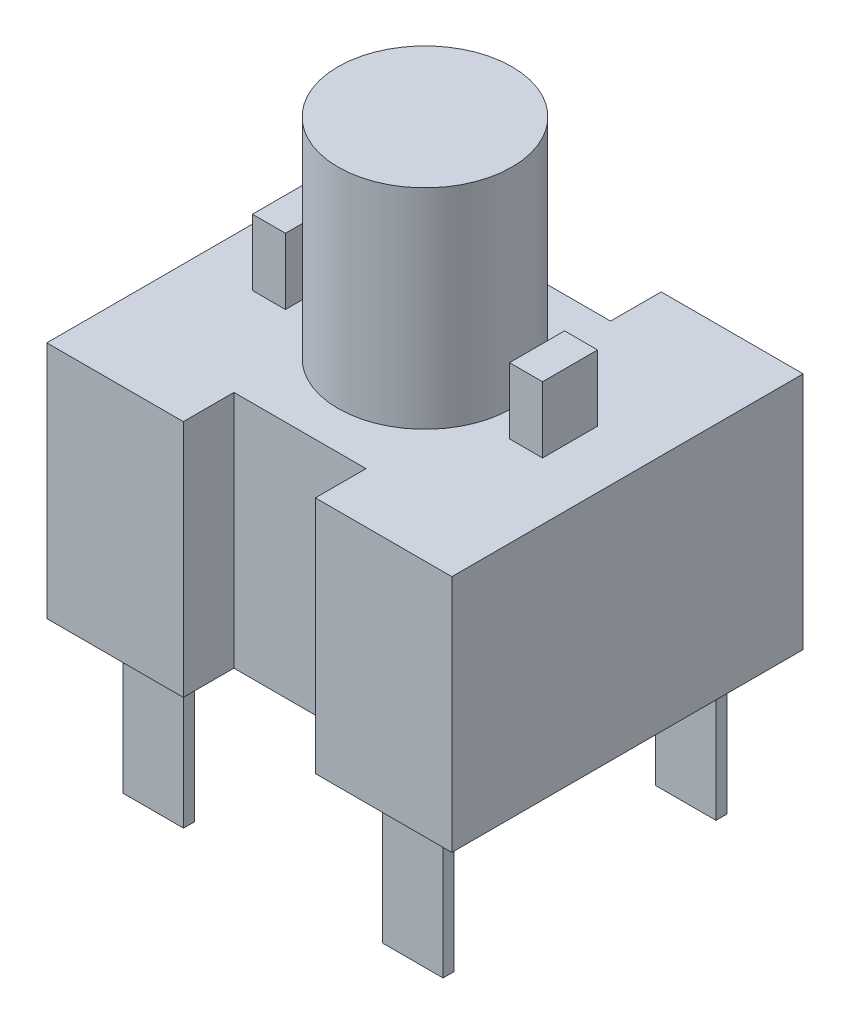
SolidWorks part; units mm, degrees
ref_plane "Front Plane" through (0, 0, 0) normal (0, 0, 1) x (1, 0, 0)
ref_plane "Top Plane" through (0, 0, 0) normal (0, 1, 0) x (1, 0, 0)
ref_plane "Right Plane" through (0, 0, 0) normal (1, 0, 0) x (0, 0, -1)
sketch "Sketch1" plane through (0, 0, 0) normal (0, 1, 0) x (1, 0, 0)
  line L1 (-9.2, -7.98) -> (9.2, -7.98)
  line L2 (-9.2, -7.98) -> (-9.2, 7.98)
  line L3 (-9.2, 7.98) -> (9.2, 7.98)
  line L4 (9.2, -7.98) -> (9.2, 7.98)
  line L5 (-9.2, -7.98) -> (9.2, 7.98) construction
  line L6 (-9.2, 7.98) -> (9.2, -7.98) construction
  point P0 (0, 0)
  dimension "D1" = 18.4
  dimension "D2" = 15.96
extrude "Boss-Extrude1" add sketch "Sketch1" along normal blind 10.85
sketch "Sketch2" plane through (0, 0, 0) normal (0, -1, 0) x (1, 0, 0)
  line L0 (0, 0) -> (-9.2, 0) construction
  line L1 (-7.27, -5.95) -> (-4.52, -5.95)
  line L2 (-7.27, -5.95) -> (-7.27, -6.45)
  line L3 (-7.27, -6.45) -> (-4.52, -6.45)
  line L4 (-4.52, -5.95) -> (-4.52, -6.45)
  line L5 (-9.2, -7.98) -> (-9.2, 7.98) construction
  line L6 (-4.52, 5.95) -> (-4.52, 6.45)
  line L7 (-7.27, 6.45) -> (-4.52, 6.45)
  line L8 (-7.27, 5.95) -> (-7.27, 6.45)
  line L9 (-7.27, 5.95) -> (-4.52, 5.95)
  line L10 (0, 0) -> (0, 7.98) construction
  line L11 (-9.2, 7.98) -> (9.2, 7.98) construction
  line L12 (4.52, -5.95) -> (4.52, -6.45)
  line L13 (7.27, -6.45) -> (4.52, -6.45)
  line L14 (7.27, -5.95) -> (7.27, -6.45)
  line L15 (7.27, -5.95) -> (4.52, -5.95)
  line L16 (7.27, 5.95) -> (4.52, 5.95)
  line L17 (7.27, 5.95) -> (7.27, 6.45)
  line L18 (7.27, 6.45) -> (4.52, 6.45)
  line L19 (4.52, 5.95) -> (4.52, 6.45)
  dimension "D1" = 0.5
  dimension "D2" = 2.75
  dimension "D3" = 12.9
  dimension "D4" = 14.54
extrude "Boss-Extrude2" add sketch "Sketch2" along normal blind 6.67
sketch "Sketch3" plane through (0, 10.85, 0) normal (0, 1, 0) x (1, 0, 0)
  line L0 (9.2, 7.98) -> (-9.2, 7.98) construction
  line L1 (-2.75, 7.98) -> (2.75, 7.98)
  line L2 (-2.75, 7.98) -> (-2.75, 5.68)
  line L3 (-2.75, 5.68) -> (2.75, 5.68)
  line L4 (2.75, 7.98) -> (2.75, 5.68)
  line L5 (-9.2, -7.98) -> (9.2, -7.98) construction
  line L6 (-3, -7.98) -> (3, -7.98)
  line L7 (-3, -7.98) -> (-3, -5.68)
  line L8 (-3, -5.68) -> (3, -5.68)
  line L9 (3, -7.98) -> (3, -5.68)
  line L10 (0, 0) -> (0, 10.6137) construction
  dimension "D1" = 2.3
  dimension "D2" = 2.3
  dimension "D3" = 5.5
  dimension "D4" = 2.75
  dimension "D5" = 6
  dimension "D6" = 3
extrude "Cut-Extrude1" cut sketch "Sketch3" against normal through all
sketch "Sketch4" plane through (0, 10.85, 0) normal (0, 1, 0) x (1, 0, 0)
  circle A0 centre (0, 0) radius 3.95
  dimension "D1" = 7.9
extrude "Boss-Extrude3" add sketch "Sketch4" along normal blind 9.5
sketch "Sketch5" plane through (0, 10.85, 0) normal (0, 1, 0) x (1, 0, 0)
  line L0 (0, 5.68) -> (0, -5.68) construction
  line L1 (-2.75, 5.68) -> (2.75, 5.68) construction
  line L2 (3, -5.68) -> (-3, -5.68) construction
  line L3 (0, 0) -> (-9.2, 0) construction
  line L4 (-6.59, 1.25) -> (-5.09, 1.25)
  line L5 (-6.59, 1.25) -> (-6.59, -1.25)
  line L6 (-6.59, -1.25) -> (-5.09, -1.25)
  line L7 (-5.09, 1.25) -> (-5.09, -1.25)
  line L8 (-9.2, 7.98) -> (-9.2, -7.98) construction
  line L9 (5.09, 1.25) -> (5.09, -1.25)
  line L10 (6.59, -1.25) -> (5.09, -1.25)
  line L11 (6.59, 1.25) -> (6.59, -1.25)
  line L12 (6.59, 1.25) -> (5.09, 1.25)
  dimension "D1" = 1.5
  dimension "D2" = 2.5
  dimension "D3" = 1.25
  dimension "D4" = 13.18
extrude "Boss-Extrude4" add sketch "Sketch5" along normal blind 3
